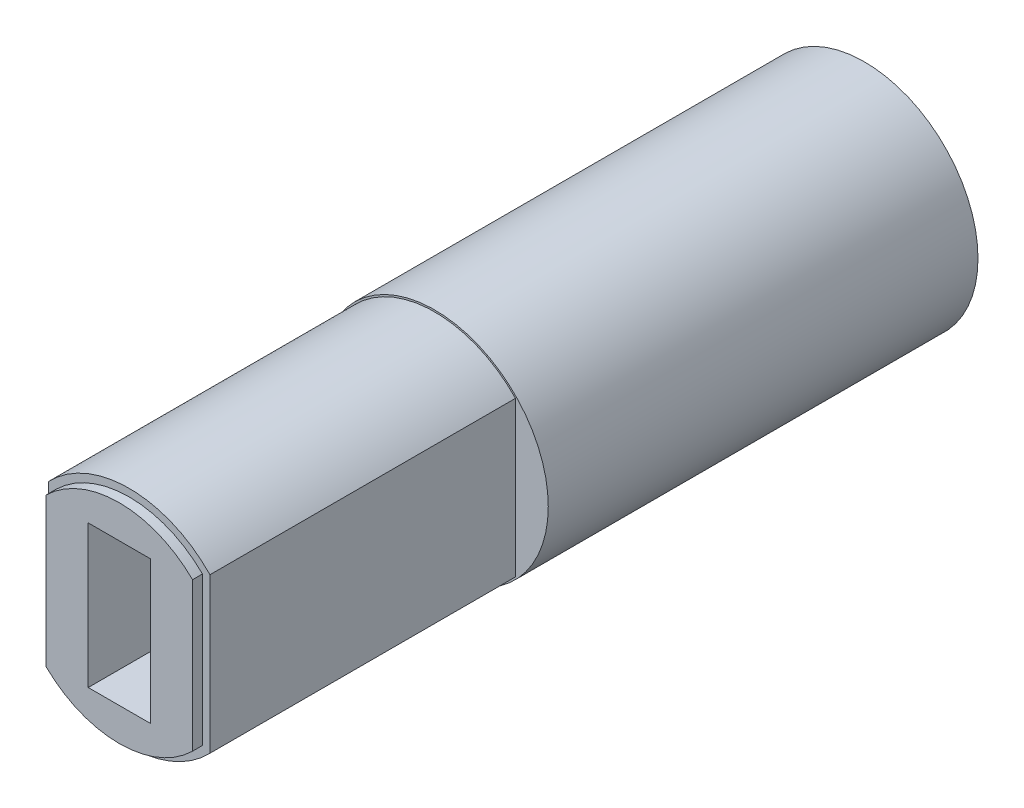
SolidWorks part; units mm, degrees
material "PF"
ref_plane "Front Plane" through (0, 0, 0) normal (0, 0, 1) x (1, 0, 0)
ref_plane "Top Plane" through (0, 0, 0) normal (0, 1, 0) x (1, 0, 0)
ref_plane "Right Plane" through (0, 0, 0) normal (1, 0, 0) x (0, 0, -1)
sketch "Sketch2" plane through (0, 0, 0) normal (0, 0, 1) x (1, 0, 0)
  circle A0 centre (0, 0) radius 4.57
  dimension "D1" = 9.14
extrude "Boss-Extrude1" add sketch "Sketch2" along normal blind 17.3
sketch "Sketch4" plane through (0, 0, 17.3) normal (0, 0, 1) x (1, 0, 0)
  line L0 (0, 0) -> (-3.25, 0) construction
  line L1 (0, 0) -> (3.25, 0) construction
  line L2 (-3.25, 3.1125) -> (-3.25, -3.1125)
  line L3 (0, 0) -> (0, 1.6894) construction
  line L4 (3.25, 3.1125) -> (3.25, -3.1125)
  arc A0 (-3.25, -3.1125) -> (3.25, -3.1125) centre (0, 0) ccw
  arc A1 (3.25, 3.1125) -> (-3.25, 3.1125) centre (0, 0) ccw
  dimension "D1" = 9
  dimension "D2" = 6.5
extrude "Boss-Extrude3" add sketch "Sketch4" along normal offset from surface (12.7 mm away) 30 up to face at (4.57, 0, 0)
sketch "Sketch5" plane through (0, 0, 30) normal (0, 0, 1) x (1, 0, 0)
  line L1 (-1.25, 2.87) -> (1.25, 2.87)
  line L2 (-1.25, 2.87) -> (-1.25, -2.87)
  line L3 (-1.25, -2.87) -> (1.25, -2.87)
  line L4 (1.25, 2.87) -> (1.25, -2.87)
  point P4 (-1.25, 0)
  point P6 (0, 2.87)
  dimension "D1" = 5.74
  dimension "D2" = 2.5
extrude "Cut-Extrude1" cut sketch "Sketch5" against normal through all
sketch "Sketch6" plane through (0, 0, 30) normal (0, 0, 1) x (1, 0, 0)
  line L0 (0, 4.2) -> (0, 4.5) construction
  line L1 (-2.95, 2.9896) -> (-2.95, -2.9896)
  line L2 (-3.25, 3.1125) -> (-3.25, -3.1125) construction
  line L3 (2.95, 2.9896) -> (2.95, -2.9896)
  line L4 (-3.25, -3.1125) -> (-3.25, 3.1125)
  line L5 (-3.25, 3.1125) -> (-3.25, -3.1125) construction
  line L6 (3.25, -3.1125) -> (3.25, 3.1125)
  arc A0 (-2.95, -2.9896) -> (2.95, -2.9896) centre (0, 0) ccw
  arc A1 (3.25, 3.1125) -> (-3.25, 3.1125) centre (0, 0) ccw construction
  arc A2 (2.95, 2.9896) -> (-2.95, 2.9896) centre (0, 0) ccw
  circle A3 centre (0, 0) radius 4.5
  dimension "D1" = 8.4
  dimension "D2" = 0.3
extrude "Cut-Extrude3" cut sketch "Sketch6" against normal blind 0.4
